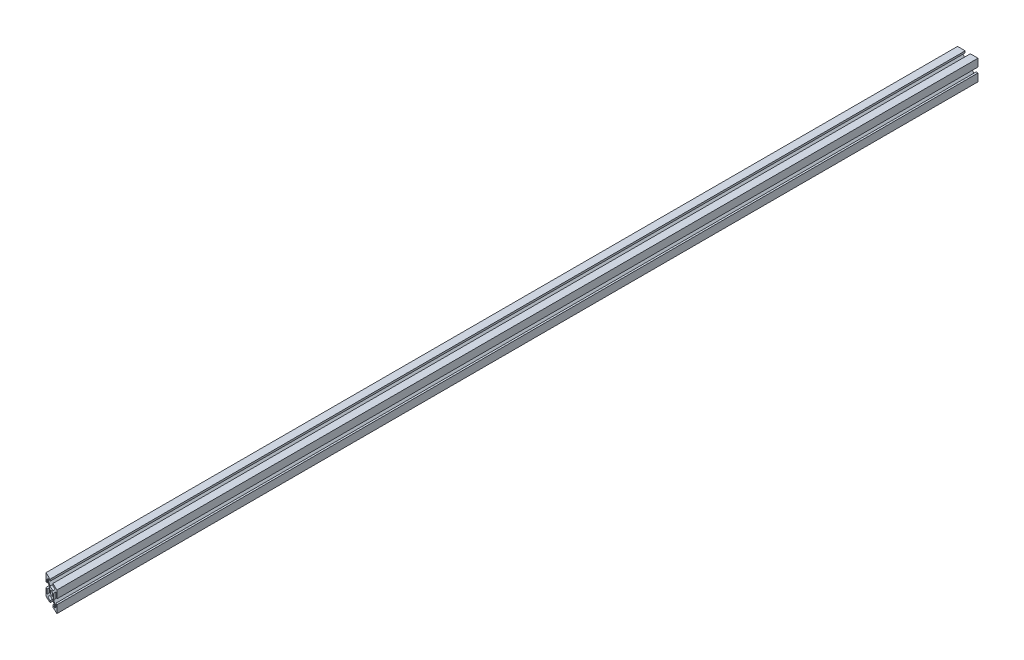
SolidWorks part; units mm, degrees
material "6063-T5"
ref_plane "Front Plane" through (0, 0, 0) normal (0, 0, 1) x (1, 0, 0)
ref_plane "Top Plane" through (0, 0, 0) normal (0, 1, 0) x (1, 0, 0)
ref_plane "Right Plane" through (0, 0, 0) normal (1, 0, 0) x (0, 0, -1)
sketch "Sketch2" plane through (0, 0, 0) normal (0, 0, 1) x (1, 0, 0)
  line L0 (-2.5, 10) -> (-2.5, 8.2)
  line L1 (-10, -10) -> (-2.5, -10)
  line L2 (-10, -10) -> (-10, -2.5)
  line L3 (-10, 10) -> (-2.5, 10)
  line L4 (10, -10) -> (10, -2.5)
  line L5 (-10, -10) -> (10, 10) construction
  line L6 (-10, 10) -> (10, -10) construction
  line L7 (-6.9272, -8.2) -> (-2.5, -8.2)
  line L8 (-8.2, -6.9272) -> (-8.2, -2.5)
  line L9 (-6.9272, 8.2) -> (-2.5, 8.2)
  line L10 (8.2, -6.9272) -> (8.2, -2.5)
  line L13 (2.5, 10) -> (2.5, 8.2)
  line L14 (2.5, 10) -> (10, 10)
  line L15 (2.5, 8.2) -> (6.9272, 8.2)
  line L16 (0, 0) -> (0, 17.5125) construction
  line L17 (-2.15, 2.15) -> (2.15, 2.15) construction
  line L18 (-2.6772, -3.95) -> (2.6772, -3.95)
  line L19 (-3.95, -2.6772) -> (-3.95, 2.6772)
  line L20 (-2.6772, 3.95) -> (2.6772, 3.95)
  line L21 (3.95, -2.6772) -> (3.95, 2.6772)
  line L24 (-2.6772, 3.95) -> (-6.9272, 8.2)
  line L25 (-3.95, 2.6772) -> (-8.2, 6.9272)
  line L26 (10, 2.5) -> (8.2, 2.5)
  line L27 (10, -2.5) -> (8.2, -2.5)
  line L28 (3.95, 2.6772) -> (8.2, 6.9272)
  line L29 (2.6772, 3.95) -> (6.9272, 8.2)
  line L30 (2.5, -10) -> (2.5, -8.2)
  line L31 (-2.5, -10) -> (-2.5, -8.2)
  line L32 (2.6772, -3.95) -> (6.9272, -8.2)
  line L33 (3.95, -2.6772) -> (8.2, -6.9272)
  line L34 (-10, -2.5) -> (-8.2, -2.5)
  line L35 (-10, 2.5) -> (-8.2, 2.5)
  line L36 (-3.95, -2.6772) -> (-8.2, -6.9272)
  line L37 (-2.6772, -3.95) -> (-6.9272, -8.2)
  line L38 (-10, 2.5) -> (-10, 10)
  line L39 (-8.2, 2.5) -> (-8.2, 6.9272)
  line L40 (10, 2.5) -> (10, 10)
  line L41 (8.2, 2.5) -> (8.2, 6.9272)
  line L42 (2.5, -8.2) -> (6.9272, -8.2)
  line L43 (2.5, -10) -> (10, -10)
  circle A0 centre (0, 0) radius 2.15
  point P0 (0, 0)
  point P54 (0, 0)
  dimension "D3" = 4.3
  dimension "D7" = 1.8
  dimension "D1" = 20
  dimension "D4" = 1.8
  dimension "D5" = 5
  dimension "D6" = 1.8
  dimension "D8" = 4
extrude "Boss-Extrude1" add sketch "Sketch2" along normal mid plane 900
sketch "Sketch3" plane through (0, 10, 0) normal (0, 1, 0) x (1, 0, 0)
  line L0 (-10, -450) -> (10, -450)
  line L1 (10, -450) -> (-10, -440.6738)
  line L2 (-10, -450) -> (-10, 450) construction
  line L3 (-10, -440.6738) -> (-10, -450)
  dimension "D1" = 25
extrude "Cut-Extrude1" cut sketch "Sketch3" against normal through all
